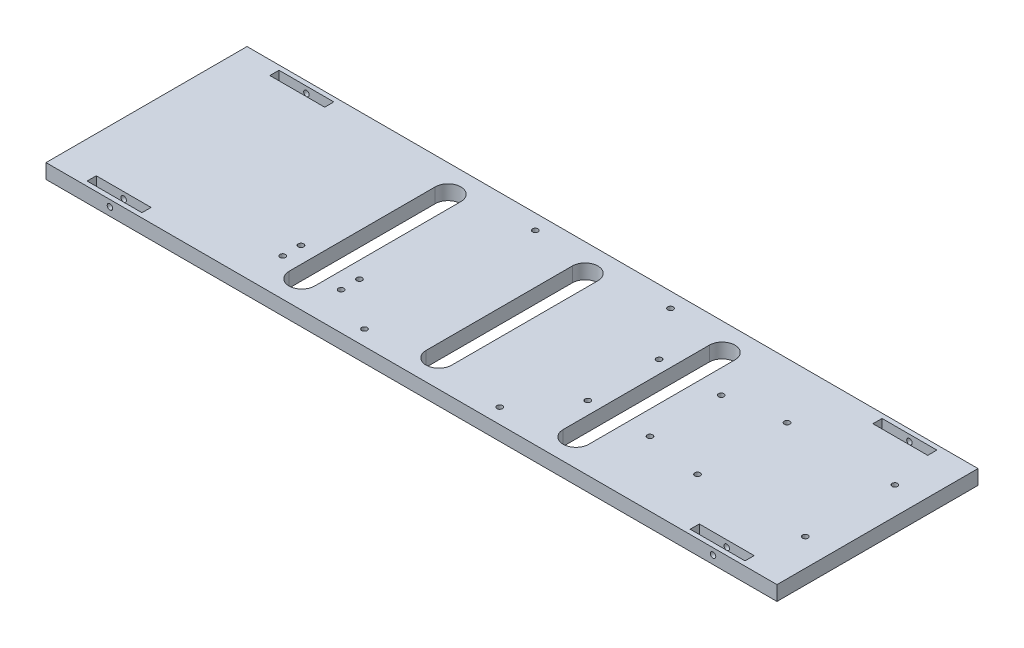
SolidWorks part; units mm, degrees
ref_plane "前视基准面" through (0, 0, 0) normal (0, 0, 1) x (1, 0, 0)
ref_plane "上视基准面" through (0, 0, 0) normal (0, 1, 0) x (1, 0, 0)
ref_plane "右视基准面" through (0, 0, 0) normal (1, 0, 0) x (0, 0, -1)
other "Configuration Table"
sketch "草图1" plane through (0, 0, 0) normal (0, 1, 0) x (1, 0, 0)
  line L1 (-200, 55) -> (200, 55)
  line L2 (-200, 55) -> (-200, -55)
  line L3 (-200, -55) -> (200, -55)
  line L4 (200, 55) -> (200, -55)
  line L5 (-200, 55) -> (200, -55) construction
  line L6 (-200, -55) -> (200, 55) construction
  point P0 (0, 0)
  dimension "D1" = 110
  dimension "D2" = 400
extrude "凸台-拉伸1" add sketch "草图1" along normal blind 8
sketch "草图2" plane through (0, 8, 0) normal (0, 1, 0) x (1, 0, 0)
  line L0 (-200, 50) -> (200, 50)
  line L1 (-200, 55) -> (-200, -55) construction
  line L2 (200, -55) -> (200, 55) construction
  line L3 (-200, -50) -> (200, -50)
  line L4 (200, 55) -> (-200, 55) construction
  line L5 (-200, -55) -> (200, -55) construction
  line L6 (-165, 55) -> (-165, -55)
  line L7 (165, 55) -> (165, -55)
  line L9 (-180, 52.5) -> (-150, 52.5)
  line L10 (-180, 52.5) -> (-180, 47.5)
  line L11 (-180, 47.5) -> (-150, 47.5)
  line L12 (-150, 52.5) -> (-150, 47.5)
  line L13 (-180, 52.5) -> (-150, 47.5) construction
  line L14 (-180, 47.5) -> (-150, 52.5) construction
  line L15 (-180, -47.5) -> (-150, -47.5)
  line L16 (-180, -47.5) -> (-180, -52.5)
  line L17 (-180, -52.5) -> (-150, -52.5)
  line L18 (-150, -47.5) -> (-150, -52.5)
  line L19 (-180, -47.5) -> (-150, -52.5) construction
  line L20 (-180, -52.5) -> (-150, -47.5) construction
  line L21 (150, 52.5) -> (180, 52.5)
  line L22 (150, 52.5) -> (150, 47.5)
  line L23 (150, 47.5) -> (180, 47.5)
  line L24 (180, 52.5) -> (180, 47.5)
  line L25 (150, 52.5) -> (180, 47.5) construction
  line L26 (150, 47.5) -> (180, 52.5) construction
  line L27 (150, -47.5) -> (180, -47.5)
  line L28 (150, -47.5) -> (150, -52.5)
  line L29 (150, -52.5) -> (180, -52.5)
  line L30 (180, -47.5) -> (180, -52.5)
  line L31 (150, -47.5) -> (180, -52.5) construction
  line L32 (150, -52.5) -> (180, -47.5) construction
  point P16 (165, 50)
  point P17 (165, -50)
  point P18 (-165, 50)
  point P19 (-165, -50)
  point P20 (-165, 50)
  point P25 (-165, -50)
  point P30 (165, 50)
  point P35 (165, -50)
  dimension "D1" = 5
  dimension "D2" = 5
  dimension "D3" = 35
  dimension "D4" = 35
  dimension "D5" = 30
  dimension "D6" = 5
  dimension "D7" = 30
  dimension "D8" = 5
  dimension "D9" = 30
  dimension "D10" = 5
  dimension "D11" = 30
  dimension "D12" = 5
extrude "切除-拉伸1" cut sketch "草图2" against normal blind 7 contours L9 L10 L0 L6 | L12 L9 L6 L0 | L12 L0 L6 L11 | L10 L11 L6 L0 | L15 L16 L3 L6 | L16 L17 L6 L3 | L18 L3 L6 L17 | L18 L15 L6 L3 | L24 L21 L7 L0 | L21 L22 L0 L7 | L22 L23 L7 L0 | L24 L0 L7 L23 | L27 L28 L3 L7 | L28 L29 L7 L3 | L30 L3 L7 L29 | L30 L27 L7 L3
sketch "草图3" plane through (0, 8, 0) normal (0, 1, 0) x (1, 0, 0)
  line L0 (-200, 0) -> (200, 0)
  line L1 (-200, 55) -> (-200, -55) construction
  line L2 (200, -55) -> (200, 55) construction
  line L3 (-75, 55) -> (-75, -55)
  line L4 (200, 55) -> (-200, 55) construction
  line L5 (-200, -55) -> (200, -55) construction
  line L6 (0, 55) -> (0, -55)
  line L7 (75, 55) -> (75, -55)
  line L8 (-75, 40) -> (-75, -40) construction
  line L9 (-68, 40) -> (-68, -40)
  line L10 (-82, 40) -> (-82, -40)
  line L11 (0, 40) -> (0, -40) construction
  line L12 (7, 40) -> (7, -40)
  line L13 (-7, 40) -> (-7, -40)
  line L14 (75, 40) -> (75, -40) construction
  line L15 (82, 40) -> (82, -40)
  line L16 (68, 40) -> (68, -40)
  arc A0 (-68, 40) -> (-82, 40) centre (-75, 40) ccw
  arc A1 (-82, -40) -> (-68, -40) centre (-75, -40) ccw
  arc A2 (7, 40) -> (-7, 40) centre (0, 40) ccw
  arc A3 (-7, -40) -> (7, -40) centre (0, -40) ccw
  arc A4 (82, 40) -> (68, 40) centre (75, 40) ccw
  arc A5 (68, -40) -> (82, -40) centre (75, -40) ccw
  point P18 (-75, 0)
  point P24 (0, 0)
  point P32 (75, 0)
  dimension "D6" = 7
  dimension "D7" = 7
  dimension "D8" = 7
  dimension "D1" = 75
  dimension "D2" = 75
  dimension "D3" = 80
  dimension "D4" = 80
  dimension "D5" = 80
  dimension "D9" = 75
extrude "切除-拉伸2" cut sketch "草图3" against normal through all contours L3 A0 L10 L0 | L9 A0 L3 L0 | L10 A1 L3 L0 | L3 A1 L9 L0 | L6 A2 L13 L0 | L12 A2 L6 L0 | L13 A3 L6 L0 | L6 A3 L12 L0 | L7 A4 L16 L0 | L15 A4 L7 L0 | L16 A5 L7 L0 | L7 A5 L15 L0
sketch "草图4" plane through (0, 8, 0) normal (0, 1, 0) x (1, 0, 0)
  line L0 (-200, 0) -> (200, 0) construction
  line L1 (-200, 55) -> (-200, -55) construction
  line L2 (200, -55) -> (200, 55) construction
  line L3 (-152, 55) -> (-152, -55)
  line L4 (200, 55) -> (-200, 55) construction
  line L5 (-200, -55) -> (200, -55) construction
  line L6 (160, 55) -> (160, -55)
  line L7 (-200, 12) -> (200, 12)
  line L8 (-200, -12) -> (200, -12)
  line L9 (-147, 55) -> (-147, -55)
  line L10 (155, 55) -> (155, -55)
  point P22 (-152, 12)
  point P23 (-147, 12)
  point P24 (-152, -12)
  point P25 (-147, -12)
  point P26 (155, 12)
  point P27 (160, 12)
  point P28 (155, -12)
  point P29 (160, -12)
  dimension "D1" = 48
  dimension "D2" = 12
  dimension "D3" = 12
  dimension "D4" = 5
  dimension "D5" = 40
  dimension "D6" = 5
sketch "草图8" plane through (0, 0, 55) normal (0, 0, 1) x (1, 0, 0)
  line L0 (-200, 4) -> (200, 4) construction
  line L1 (-200, 8) -> (-200, 0) construction
  line L2 (200, 8) -> (200, 0) construction
  line L3 (-165, 8) -> (-165, 0) construction
  line L4 (-200, 8) -> (200, 8) construction
  line L5 (-200, 0) -> (200, 0) construction
  line L6 (165, 8) -> (165, 0) construction
  line L7 (200, 4.5) -> (-200, 4.5) construction
  line L8 (-200, 8) -> (200, 8) construction
  circle A0 centre (165, 4.5) radius 1.5
  circle A1 centre (-165, 4.5) radius 1.5
  point P18 (-165, 4.5)
  point P19 (165, 4.5)
  dimension "D4" = 3
  dimension "D1" = 35
  dimension "D2" = 35
  dimension "D3" = 3.5
extrude "切除-拉伸4" cut sketch "草图8" against normal through all
sketch "草图11" plane through (0, 8, 0) normal (0, 1, 0) x (1, 0, 0)
  line L0 (-202.0957, 0) -> (200, 0) construction
  line L1 (200, -55) -> (200, 55) construction
  line L2 (-200, 24.5) -> (200, 24.5) construction
  line L3 (-200, 55) -> (-200, -55) construction
  line L4 (-200, -24.5) -> (200, -24.5) construction
  line L5 (200, 55) -> (-200, 55) construction
  line L6 (185, 55) -> (185, -55) construction
  line L7 (-200, -55) -> (200, -55) construction
  line L8 (126, 55) -> (126, -55) construction
  circle A0 centre (126, 24.5) radius 1.5
  circle A1 centre (185, 24.5) radius 1.5
  circle A2 centre (185, -24.5) radius 1.5
  circle A3 centre (126, -24.5) radius 1.5
  point P18 (185, -24.5)
  point P19 (126, -24.5)
  point P20 (185, 24.5)
  point P21 (126, 24.5)
  dimension "D5" = 3
  dimension "D1" = 49
  dimension "D2" = 30.5
  dimension "D3" = 59
  dimension "D4" = 15
extrude "切除-拉伸6" cut sketch "草图11" against normal blind 10
sketch "草图12" plane through (0, 8, 0) normal (0, 1, 0) x (1, 0, 0)
  line L0 (-200, 0) -> (200, 0) construction
  line L1 (-200, 55) -> (-200, -55) construction
  line L2 (200, -55) -> (200, 55) construction
  line L3 (-200, 19.5) -> (200, 19.5) construction
  line L4 (-200, -19.5) -> (200, -19.5) construction
  line L5 (200, 55) -> (-200, 55) construction
  line L6 (95, 55) -> (95, -55) construction
  line L7 (-200, -55) -> (200, -55) construction
  line L8 (61, 55) -> (61, -55) construction
  circle A0 centre (61, 19.5) radius 1.5
  circle A1 centre (95, 19.5) radius 1.5
  circle A2 centre (95, -19.5) radius 1.5
  circle A3 centre (61, -19.5) radius 1.5
  point P18 (61, 19.5)
  point P19 (95, 19.5)
  point P20 (95, 0)
  point P21 (61, 0)
  point P22 (61, -19.5)
  point P23 (95, -19.5)
  point P32 (61, 19.5)
  dimension "D5" = 3
  dimension "D1" = 39
  dimension "D2" = 35.5
  dimension "D3" = 34
  dimension "D4" = 105
extrude "切除-拉伸7" cut sketch "草图12" against normal blind 10
sketch "草图13" plane through (0, 8, 0) normal (0, 1, 0) x (1, 0, 0)
  line L0 (-200, 0) -> (200, 0) construction
  line L1 (-200, 55) -> (-200, -55) construction
  line L2 (200, -55) -> (200, 55) construction
  line L3 (-200, 46.75) -> (200, 46.75) construction
  line L4 (-200, -46.75) -> (200, -46.75) construction
  line L5 (-200, -55) -> (200, -55) construction
  line L6 (-34, 55) -> (-34, -55) construction
  line L7 (200, 55) -> (-200, 55) construction
  line L8 (40, 55) -> (40, -55) construction
  circle A0 centre (-34, 46.75) radius 1.5
  circle A1 centre (40, 46.75) radius 1.5
  circle A2 centre (40, -46.75) radius 1.5
  circle A3 centre (-34, -46.75) radius 1.5
  point P18 (-34, 46.75)
  point P19 (40, 46.75)
  point P21 (40, -46.75)
  point P22 (-34, -46.75)
  dimension "D5" = 3
  dimension "D1" = 93.5
  dimension "D2" = 8.25
  dimension "D3" = 74
  dimension "D4" = 160
extrude "切除-拉伸8" cut sketch "草图13" against normal blind 10
sketch "草图14" plane through (0, 8, 0) normal (0, 1, 0) x (1, 0, 0)
  line L0 (-200, 11) -> (200, 11) construction
  line L1 (-200, 55) -> (-200, -55) construction
  line L2 (200, -55) -> (200, 55) construction
  line L3 (-200, -11) -> (200, -11) construction
  line L4 (-59, 55) -> (-59, -55) construction
  line L5 (200, 55) -> (-200, 55) construction
  line L6 (-200, -55) -> (200, -55) construction
  line L7 (-91, 55) -> (-91, -55) construction
  line L8 (-200, 0) -> (200, 0) construction
  line L9 (-200, -43) -> (200, -43) construction
  line L10 (-200, -34.5) -> (200, -34.5) construction
  line L11 (-200, -24.5) -> (200, -24.5) construction
  circle A0 centre (-91, -24.5) radius 1.5
  circle A1 centre (-91, -34.5) radius 1.5
  circle A2 centre (-59, -34.5) radius 1.5
  circle A3 centre (-59, -24.5) radius 1.5
  point P24 (-91, -24.5)
  point P25 (-91, -34.5)
  point P26 (-59, -24.5)
  point P27 (-59, -34.5)
  dimension "D8" = 3
  dimension "D1" = 22
  dimension "D2" = 11
  dimension "D3" = 32
  dimension "D4" = 32
  dimension "D5" = 8.5
  dimension "D6" = 10
  dimension "D7" = 109
extrude "切除-拉伸9" cut sketch "草图14" against normal through all
